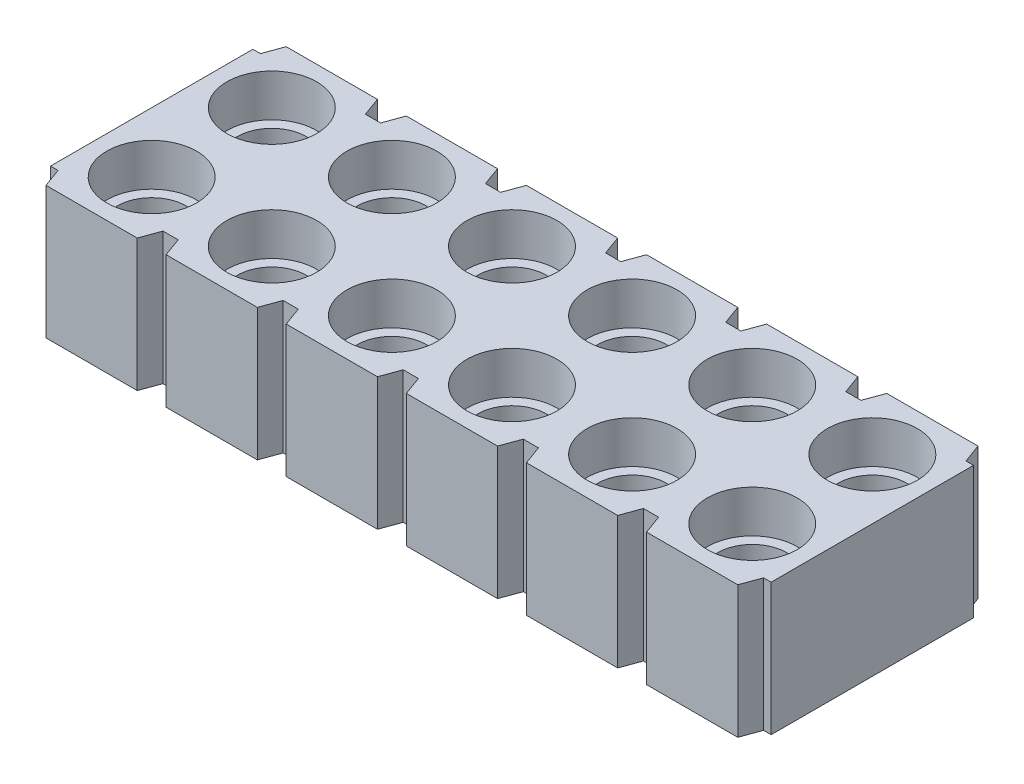
SolidWorks part; units mm, degrees
material "PCT Polyester"
ref_plane "Front Plane" through (0, 0, 0) normal (0, 0, 1) x (1, 0, 0)
ref_plane "Top Plane" through (0, 0, 0) normal (0, 1, 0) x (1, 0, 0)
ref_plane "Right Plane" through (0, 0, 0) normal (1, 0, 0) x (0, 0, -1)
sketch "Sketch1" plane through (0, 0, 0) normal (0, 1, 0) x (1, 0, 0)
  line L0 (14.9344, 0.4) -> (14.7744, 0.4)
  line L1 (14.9344, 4.6799) -> (14.9344, 0.4)
  line L2 (-0.3056, 4.6799) -> (-0.1456, 4.6799)
  line L3 (-0.3056, 4.6799) -> (-0.3056, 0.4)
  line L4 (0, 0) -> (14.6287, 0)
  line L5 (0, 5.08) -> (-0.1456, 4.6799)
  line L6 (0, 0) -> (-0.1456, 0.4)
  line L7 (-0.3056, 0.4) -> (-0.1456, 0.4)
  line L9 (14.6287, 0) -> (14.7744, 0.4)
  line L10 (14.6287, 5.08) -> (14.7744, 4.6799)
  line L11 (14.9344, 4.6799) -> (14.7744, 4.6799)
  line L16 (14.6287, 5.08) -> (0, 5.08)
  dimension "D2" = 5.08
  dimension "D3" = 20
  dimension "D4" = 0.4
  dimension "D5" = 0.4
  dimension "D7" = 0.16
  dimension "INSLENGTH" = 15.24
extrude "Extrude1" add sketch "Sketch1" against normal blind 2.794
hole_wizard "Hole1" positions "3DSketch2" profile "Sketch3" legacy end condition through all
sketch3d "3DSketch2"
  line L4 (0, 0, 0) -> (14.6287, 0, 0) construction
  line L5 (-0.3056, 0, -4.6799) -> (-0.3056, 0, -0.4) construction
  point P0 (0.9644, 0, -1.27)
  dimension "D1" = 1.27
  dimension "D2" = 1.27
sketch "Sketch3" plane through (0.9644, 0, -1.27) normal (1, 0, 0) x (0, 0, 1)
  line L0 (0, 0) -> (0, 2.794)
  line L1 (0, 2.794) -> (0.73, 2.794)
  line L2 (0.73, 2.794) -> (0.73, 0.8941)
  line L3 (0.73, 0.8941) -> (0.95, 0.8941)
  line L4 (0.95, 0.8941) -> (0.95, 0)
  line L5 (0.95, 0) -> (0, 0)
  line L6 (0, 110) -> (0, -10) construction
  dimension "Diameter" = 1.46
  dimension "Depth" = 2.794
  dimension "C-Bore Diameter" = 1.8999
  dimension "C-Bore Depth" = 0.8941
sketch "Sketch4" plane through (0, 0, 0) normal (0, 1, 0) x (1, 0, 0)
  line L0 (1.9288, 0) -> (2.54, 0)
  line L2 (0, 0) -> (14.6287, 0) construction
  line L5 (2.0744, 0.4) -> (1.9288, 0)
  line L6 (2.3944, 0.4) -> (2.54, 0)
  line L7 (14.6287, 5.08) -> (0, 5.08) construction
  line L8 (2.0744, 0.4) -> (2.3944, 0.4)
  line L10 (2.0744, 4.6799) -> (2.3944, 4.6799)
  line L11 (2.3944, 4.6799) -> (2.54, 5.08)
  line L12 (2.0744, 4.6799) -> (1.9288, 5.08)
  line L13 (1.9288, 5.08) -> (2.54, 5.08)
  line L17 (-0.3056, 4.6799) -> (-0.3056, 0.4) construction
  dimension "D1" = 0.4
  dimension "D2" = 0.32
  dimension "D3" = 70
  dimension "D4" = 0.6112
  dimension "D5" = 0.4001
  dimension "D6" = 2.2344
extrude "Extrude2" cut sketch "Sketch4" against normal blind 2.794
pattern_linear "Hole Pattern" count 32 spacing 2.54 along (1, 0, 0) count 2 spacing 2.54 along (0, 0, -1) of "Hole1"
pattern_linear "Slot Pattern" count 31 spacing 2.54 along (1, 0, 0) of "Extrude2"
